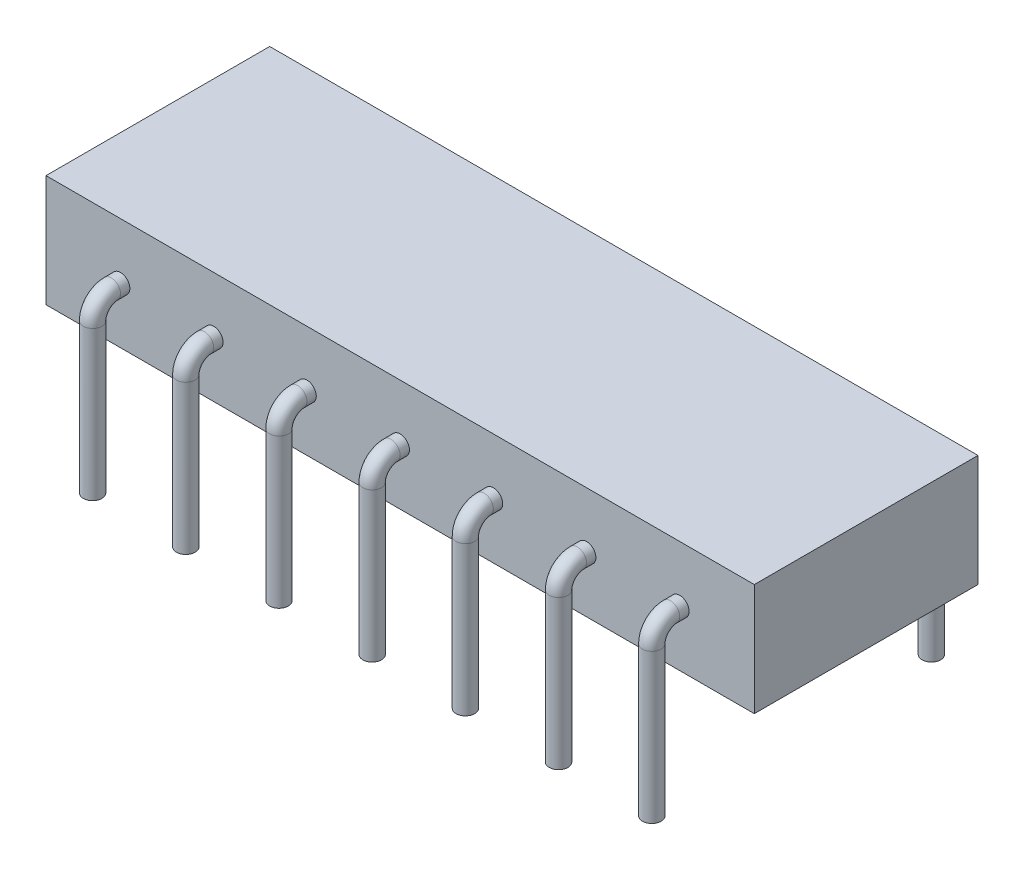
SolidWorks part; units mm, degrees
ref_plane "Front" through (0, 0, 0) normal (0, 0, 1) x (1, 0, 0)
ref_plane "Top" through (0, 0, 0) normal (0, 1, 0) x (1, 0, 0)
ref_plane "Right" through (0, 0, 0) normal (1, 0, 0) x (0, 0, -1)
sketch "Sketch1" plane through (0, 0, 0) normal (0, 1, 0) x (1, 0, 0)
  line L0 (0, 0) -> (0, 6)
  line L1 (0, 6) -> (19, 6)
  line L2 (19, 6) -> (19, 0)
  line L3 (19, 0) -> (0, 0)
  dimension "D1" = 6
  dimension "D2" = 19
extrude "Boss-Extrude1" add sketch "Sketch1" along normal blind 3
ref_plane "Plane1" through (0, 0, -3) normal (0, 0, 1) x (1, 0, 0)
sketch "Sketch3" plane through (0, 0, 0) normal (0, 0, 1) x (1, 0, 0)
  line L0 (0, 3) -> (0, 0) construction
  line L1 (0, 0) -> (19, 0) construction
  circle A0 centre (2, 1.5) radius 0.25
  dimension "D1" = 0.5
  dimension "D2" = 2
  dimension "D3" = 1.5
ref_plane "Plane2" through (2, 0, 0) normal (1, 0, 0) x (0, 0, -1)
sketch "Sketch4" plane through (2, 0, 0) normal (1, 0, 0) x (0, 0, -1)
  line L0 (0, 1.5) -> (-0.25, 1.5)
  line L1 (0, 1.75) -> (0, 1.25) construction
  line L2 (-0.75, 1) -> (-0.75, -3)
  arc A0 (-0.25, 1.5) -> (-0.75, 1) centre (-0.25, 1) ccw
  dimension "D2" = 0.5
  dimension "D1" = 0.25
  dimension "D3" = 4
sweep "Sweep1" add profiles "Sketch3" path "Sketch4"
pattern_linear "LPattern1" count 7 spacing 2.5 along (1, 0, 0) of "Sweep1"
mirror "Mirror1" about plane through (0, 0, -3) normal (0, 0, 1) of "LPattern1", "Sweep1"
